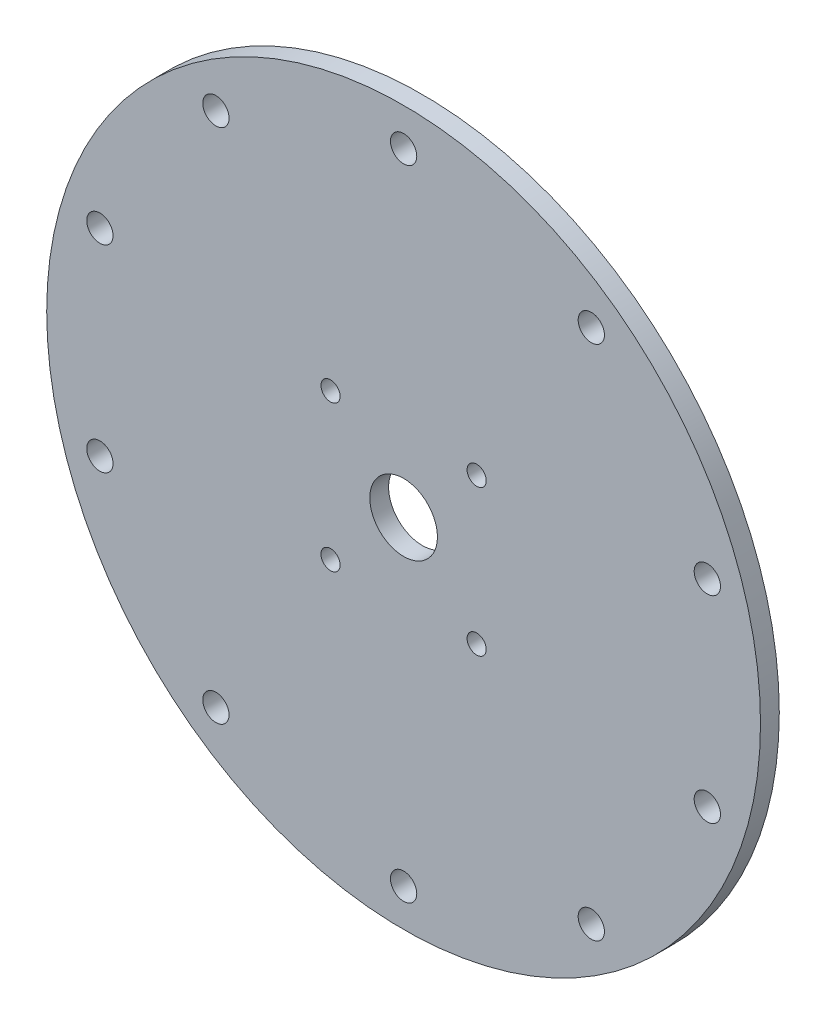
SolidWorks part; units mm, degrees
ref_plane "Ön Düzlem" through (0, 0, 0) normal (0, 0, 1) x (1, 0, 0)
ref_plane "Üst Düzlem" through (0, 0, 0) normal (0, 1, 0) x (1, 0, 0)
ref_plane "Sağ Düzlem" through (0, 0, 0) normal (1, 0, 0) x (0, 0, -1)
sketch "Çizim1" plane through (0, 0, 0) normal (0, 0, 1) x (1, 0, 0)
  line L1 (-38.8909, 38.8909) -> (38.8909, 38.8909) construction
  line L2 (-38.8909, 38.8909) -> (-38.8909, -38.8909) construction
  line L3 (-38.8909, -38.8909) -> (38.8909, -38.8909) construction
  line L4 (38.8909, 38.8909) -> (38.8909, -38.8909) construction
  line L5 (-38.8909, 38.8909) -> (38.8909, -38.8909) construction
  line L6 (-38.8909, -38.8909) -> (38.8909, 38.8909) construction
  line L7 (-60, -60) -> (60, -60) construction
  line L8 (-60, -60) -> (-60, 60) construction
  line L9 (-60, 60) -> (60, 60) construction
  line L10 (60, -60) -> (60, 60) construction
  line L11 (-60, -60) -> (60, 60) construction
  line L12 (-60, 60) -> (60, -60) construction
  circle A0 centre (0, 0) radius 190
  circle A1 centre (0, 0) radius 170 construction
  circle A2 centre (0, 170) radius 7
  circle A3 centre (-99.9235, 137.5329) radius 7
  circle A4 centre (-161.6796, 52.5329) radius 7
  circle A5 centre (-161.6796, -52.5329) radius 7
  circle A6 centre (-99.9235, -137.5329) radius 7
  circle A7 centre (0, -170) radius 7
  circle A8 centre (99.9235, -137.5329) radius 7
  circle A9 centre (161.6796, -52.5329) radius 7
  circle A10 centre (161.6796, 52.5329) radius 7
  circle A11 centre (99.9235, 137.5329) radius 7
  circle A12 centre (0, 0) radius 18
  circle A13 centre (-38.8909, 38.8909) radius 5.1
  circle A14 centre (38.8909, 38.8909) radius 5.1
  circle A15 centre (38.8909, -38.8909) radius 5.1
  circle A16 centre (-38.8909, -38.8909) radius 5.1
  circle A17 centre (0, 0) radius 55 construction
  point P26 (0, 0)
  dimension "D1" = 380
  dimension "D2" = 340
  dimension "D3" = 14
  dimension "D5" = 36
  dimension "D6" = 110
  dimension "D7" = 10.2
  dimension "D8" = 120
  dimension "D4" = 10
extrude "Yükseklik-Ekstrüzyon1" add sketch "Çizim1" along normal blind 10
